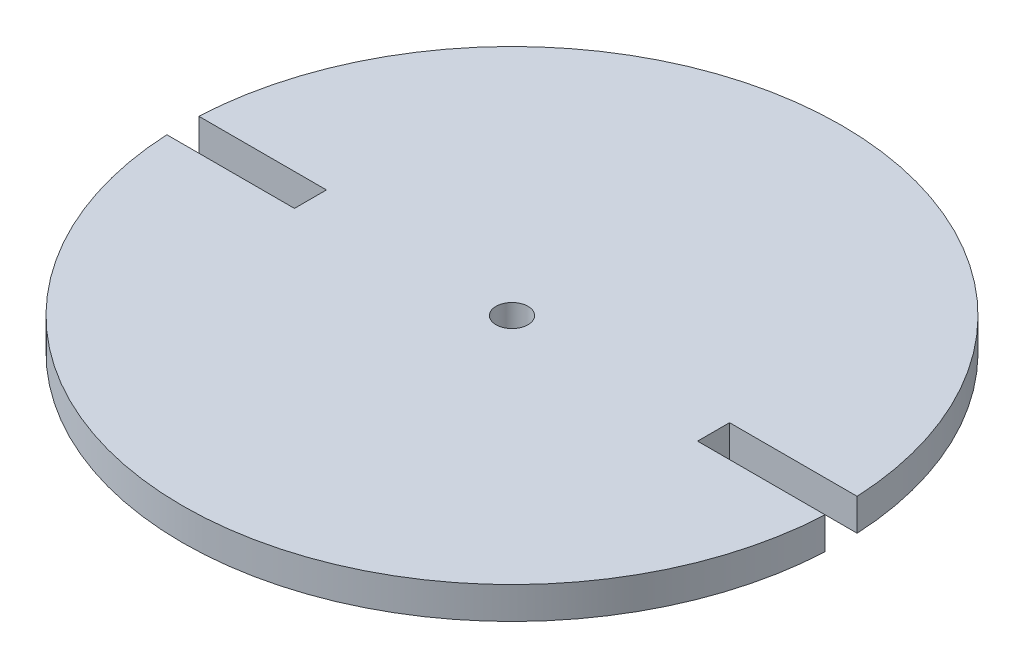
SolidWorks part; units mm, degrees
material "E-Glass Fiber"
ref_plane "Front Plane" through (0, 0, 0) normal (0, 0, 1) x (1, 0, 0)
ref_plane "Top Plane" through (0, 0, 0) normal (0, 1, 0) x (1, 0, 0)
ref_plane "Right Plane" through (0, 0, 0) normal (1, 0, 0) x (0, 0, -1)
sketch "Sketch1" plane through (0, 0, 0) normal (0, 1, 0) x (1, 0, 0)
  circle A0 centre (0, 0) radius 65.405
  dimension "D1" = 130.81
extrude "Boss-Extrude1" add sketch "Sketch1" along normal blind 6.35
sketch "Sketch2" plane through (0, 6.35, 0) normal (0, 1, 0) x (1, 0, 0)
  line L1 (-90.805, -3.175) -> (-40.005, -3.175)
  line L2 (-90.805, -3.175) -> (-90.805, 3.175)
  line L3 (-90.805, 3.175) -> (-40.005, 3.175)
  line L4 (-40.005, -3.175) -> (-40.005, 3.175)
  line L5 (-90.805, -3.175) -> (-40.005, 3.175) construction
  line L6 (-90.805, 3.175) -> (-40.005, -3.175) construction
  line L7 (90.805, 3.175) -> (40.005, 3.175)
  line L8 (90.805, 3.175) -> (90.805, -3.175)
  line L9 (90.805, -3.175) -> (40.005, -3.175)
  line L10 (40.005, 3.175) -> (40.005, -3.175)
  line L11 (90.805, 3.175) -> (40.005, -3.175) construction
  line L12 (90.805, -3.175) -> (40.005, 3.175) construction
  circle A0 centre (0, 0) radius 65.405 construction
  point P0 (-65.405, 0)
  point P7 (65.405, 0)
  dimension "D1" = 50.8
  dimension "D2" = 6.35
  dimension "D3" = 50.8
  dimension "D4" = 6.35
extrude "Cut-Extrude1" cut sketch "Sketch2" against normal blind 6.35
sketch "Sketch4" plane through (0, 6.35, 0) normal (0, 1, 0) x (1, 0, 0)
  line L0 (-65.8212, 0) -> (65.1154, 0) construction
  line L1 (0, 65.405) -> (0, -65.405) construction
  arc A0 (65.3279, 3.175) -> (-65.3279, 3.175) centre (0, 0) ccw construction
  arc A1 (-65.3279, -3.175) -> (65.3279, -3.175) centre (0, 0) ccw construction
sketch "Sketch7" plane through (0, 6.35, 0) normal (0, 1, 0) x (1, 0, 0)
  circle A0 centre (0, 0) radius 3.175
extrude "Cut-Extrude2" cut sketch "Sketch7" against normal through all
